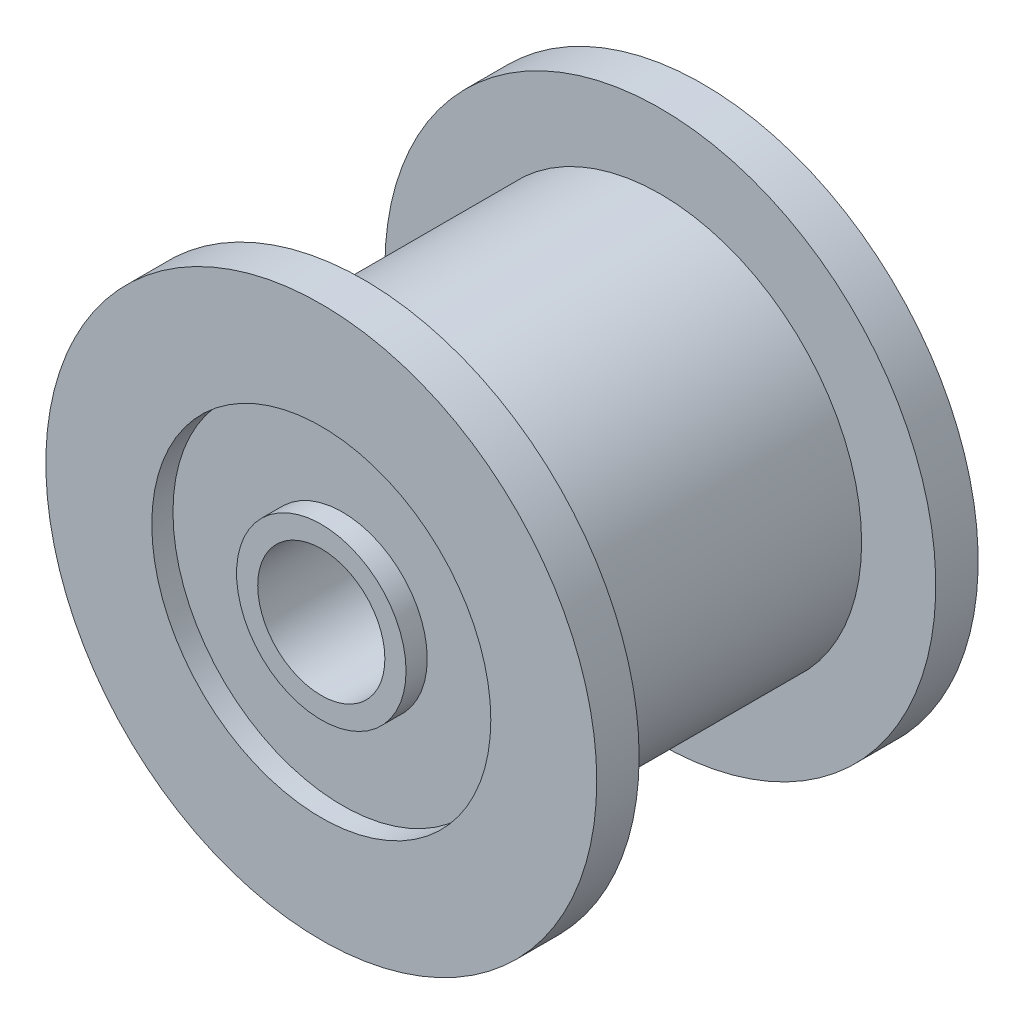
SolidWorks part; units mm, degrees
ref_plane "前视基准面" through (0, 0, 0) normal (0, 0, 1) x (1, 0, 0)
ref_plane "上视基准面" through (0, 0, 0) normal (0, 1, 0) x (1, 0, 0)
ref_plane "右视基准面" through (0, 0, 0) normal (1, 0, 0) x (0, 0, -1)
sketch "草图1" plane through (0, 0, 0) normal (0, 0, 1) x (1, 0, 0)
  circle A0 centre (0, 0) radius 4.75
extrude "凸台-拉伸1" add sketch "草图1" along normal blind 7
sketch "草图2" plane through (0, 0, 7) normal (0, 0, 1) x (1, 0, 0)
  circle A0 centre (0, 0) radius 6.5
extrude "凸台-拉伸2" add sketch "草图2" along normal blind 1
sketch "草图3" plane through (0, 0, 0) normal (0, 0, -1) x (-1, 0, 0)
  circle A0 centre (0, 0) radius 6.5
extrude "凸台-拉伸3" add sketch "草图3" along normal blind 1
sketch "草图4" plane through (0, 0, -1) normal (0, 0, -1) x (-1, 0, 0)
  circle A0 centre (0, 0) radius 1.5
extrude "切除-拉伸1" cut sketch "草图4" against normal blind 12
sketch "草图5" plane through (0, 0, -1) normal (0, 0, -1) x (-1, 0, 0)
  circle A0 centre (0, 0) radius 2
  circle A1 centre (0, 0) radius 4
extrude "切除-拉伸2" cut sketch "草图5" against normal blind 0.5
sketch "草图6" plane through (0, 0, 8) normal (0, 0, 1) x (1, 0, 0)
  circle A0 centre (0, 0) radius 2
  circle A1 centre (0, 0) radius 4
extrude "切除-拉伸3" cut sketch "草图6" against normal blind 0.5
